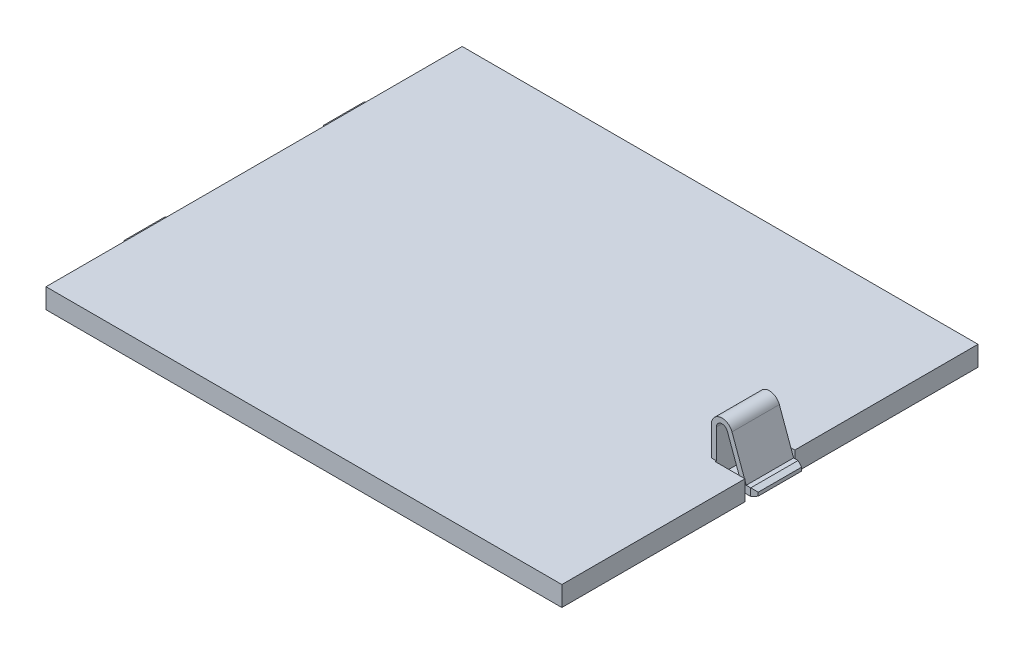
SolidWorks part; units mm, degrees
ref_plane "Front Plane" through (0, 0, 0) normal (0, 0, 1) x (1, 0, 0)
ref_plane "Top Plane" through (0, 0, 0) normal (0, 1, 0) x (1, 0, 0)
ref_plane "Right Plane" through (0, 0, 0) normal (1, 0, 0) x (0, 0, -1)
sketch "Sketch1" plane through (0, 0, 0) normal (0, 1, 0) x (1, 0, 0)
  line L0 (-51.75, 24.75) -> (-51.75, 41.75)
  line L1 (-51.75, -41.75) -> (51.75, -41.75)
  line L2 (-51.75, -41.75) -> (-51.75, -24.75)
  line L3 (-51.75, 41.75) -> (51.75, 41.75)
  line L4 (51.75, -41.75) -> (51.75, 41.75)
  line L5 (-51.75, -41.75) -> (51.75, 41.75) construction
  line L6 (-51.75, 41.75) -> (51.75, -41.75) construction
  line L7 (-51.75, 24.75) -> (-53.75, 24.75)
  line L9 (-51.75, 15.25) -> (-53.75, 15.25)
  line L10 (-53.75, 24.75) -> (-53.75, 15.25)
  line L11 (-51.75, -15.25) -> (-53.75, -15.25)
  line L13 (-51.75, -24.75) -> (-53.75, -24.75)
  line L14 (-53.75, -15.25) -> (-53.75, -24.75)
  line L15 (-51.75, -15.25) -> (-51.75, 15.25)
  line L16 (-53.75, -15.25) -> (-53.75, 15.25) construction
  point P0 (0, 0)
  point P14 (-53.75, 0)
  point P15 (-1369.06, 313.084)
  point P16 (-53.75, 20)
  point P17 (-53.75, -20)
  dimension "D1" = 9.5
  dimension "D2" = 2
  dimension "D3" = 103.5
  dimension "D4" = 83.5
  dimension "D5" = 40
extrude "Boss-Extrude1" add sketch "Sketch1" along normal blind 4
sketch "Sketch3" plane through (0, 4, 0) normal (0, 1, 0) x (1, 0, 0)
  line L0 (51.75, -41.75) -> (51.75, 41.75) construction
  line L1 (51.75, 5) -> (45.75, 5)
  line L2 (51.75, 5) -> (51.75, -5)
  line L3 (51.75, -5) -> (45.75, -5)
  line L4 (45.75, 5) -> (45.75, -5)
  point P6 (45.75, 0)
  dimension "D1" = 10
  dimension "D2" = 6
extrude "Cut-Extrude1" cut sketch "Sketch3" against normal up to next
sketch "Sketch4" plane through (0, 0, 0) normal (0, 0, 1) x (1, 0, 0)
  line L0 (45.75, 4) -> (45.75, 9.863)
  line L1 (48.895, 10.5939) -> (51.75, 2.75)
  line L2 (51.75, 2.75) -> (53.75, 2.75)
  line L3 (53.75, 2.75) -> (53.75, 1.25)
  line L4 (53.75, 1.25) -> (48.25, 1.25)
  line L5 (48.25, 1.25) -> (48.25, 3.75)
  line L6 (48.25, 3.75) -> (50.3219, 3.75)
  line L7 (50.3219, 3.75) -> (47.9554, 10.2519)
  line L8 (44.75, 4) -> (44.75, 9.863)
  line L9 (44.75, 4) -> (45.75, 4)
  line L10 (51.75, 0) -> (51.75, 4) construction
  line L11 (51.75, 0) -> (51.75, 4)
  arc A0 (44.75, 9.863) -> (48.895, 10.5939) centre (46.887, 9.863) cw
  arc A1 (45.75, 9.863) -> (47.9554, 10.2519) centre (46.887, 9.863) cw
  point P17 (53.75, 2)
  point P18 (51.75, 2)
  point P19 (52.5861, 2.75)
  point P20 (50.9086, 2.75)
  dimension "D1" = 1
  dimension "D2" = 1.5
  dimension "D3" = 2
  dimension "D4" = 7
  dimension "D5" = 2
  dimension "D6" = 2.5
  dimension "D7" = 20
  dimension "D8" = 2.5
extrude "Boss-Extrude2" add sketch "Sketch4" along normal blind 4.75 and the other way blind 4.75 contours L0 A1 L7 L6 L5 L4 L11 L1 A0 L8 L9 | L11 L4 L3 L2
sketch "Sketch5" plane through (0, 1.25, 0) normal (0, -1, 0) x (1, 0, 0)
  line L1 (48.75, 3) -> (51.75, 3)
  line L2 (48.75, 3) -> (48.75, -3)
  line L3 (48.75, -3) -> (51.75, -3)
  line L4 (51.75, 3) -> (51.75, -3)
  line L5 (48.75, 3) -> (51.75, -3) construction
  line L6 (48.75, -3) -> (51.75, 3) construction
  line L7 (51.75, -5) -> (51.75, -41.75) construction
  point P0 (50.25, 0)
  point P9 (0, 0)
  dimension "D1" = 6
  dimension "D2" = 3
extrude "Cut-Extrude2" cut sketch "Sketch5" against normal blind 0.8
sketch "Sketch6" plane through (0, 0, 24.75) normal (0, 0, 1) x (1, 0, 0)
  line L0 (-53.75, 4) -> (-53.75, 0) construction
  line L1 (-51.75, 4) -> (-53.75, 4)
  line L2 (-51.75, 4) -> (-51.75, 2.9)
  line L3 (-51.75, 2.9) -> (-53.75, 2.9)
  line L4 (-53.75, 4) -> (-53.75, 2.9)
  line L5 (-53.75, 1.1) -> (-53.75, 2.9) construction
  line L6 (-51.75, 0) -> (-53.75, 0)
  line L7 (-51.75, 0) -> (-51.75, 1.1)
  line L8 (-51.75, 1.1) -> (-53.75, 1.1)
  line L9 (-53.75, 0) -> (-53.75, 1.1)
  line L10 (-51.75, 4) -> (-51.75, 0) construction
  point P14 (-51.75, 2)
  point P15 (-53.75, 2)
  dimension "D1" = 1.1
extrude "Cut-Extrude3" cut sketch "Sketch6" against normal through all
chamfer "Chamfer3" distance 0.4 angle 70 4 edges at (53.75, 2, -4.75) (53.75, 1.25, 0) (53.75, 2, 4.75) (53.75, 2.75, 0)
chamfer "Chamfer4" distance 0.7 angle 70 8 edges at (-53.75, 2, 15.25) (-53.75, 1.1, 20) (-53.75, 2, 24.75) (-53.75, 2.9, 20) (-53.75, 2, -24.75) (-53.75, 1.1, -20) (-53.75, 2, -15.25) (-53.75, 2.9, -20)
